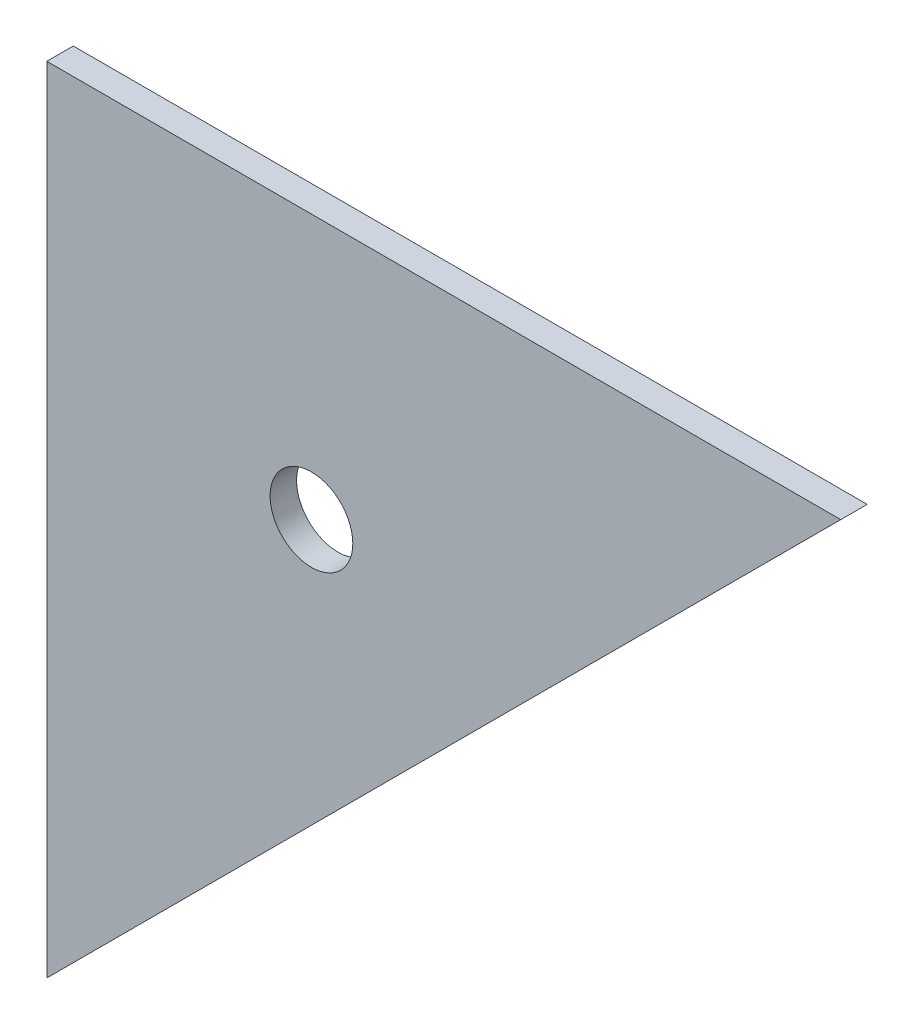
SolidWorks part; units mm, degrees
ref_plane "Front" through (0, 0, 0) normal (0, 0, 1) x (1, 0, 0)
ref_plane "Top" through (0, 0, 0) normal (0, 1, 0) x (1, 0, 0)
ref_plane "Right" through (0, 0, 0) normal (1, 0, 0) x (0, 0, -1)
sketch "Sketch1" plane through (0, 0, 0) normal (0, 0, 1) x (1, 0, 0)
  line L0 (-5.2668, 29.0495) -> (70.9332, 29.0495)
  line L1 (70.9332, 29.0495) -> (-5.2668, -47.1505)
  line L2 (-5.2668, -47.1505) -> (-5.2668, 29.0495)
extrude "Boss-Extrude1" add sketch "Sketch1" along normal blind 2.54
sketch "Sketch3" plane through (0, 0, 2.54) normal (0, 0, 1) x (1, 0, 0)
  line L0 (20.1332, 29.0495) -> (20.1332, -21.7505) construction
  line L1 (70.9332, 29.0495) -> (-5.2668, 29.0495) construction
  line L2 (-5.2668, -47.1505) -> (70.9332, 29.0495) construction
  line L3 (-5.2668, 3.6495) -> (38.3694, 3.6495) construction
  line L4 (-5.2668, 29.0495) -> (-5.2668, -47.1505) construction
  circle A0 centre (20.1332, 3.6495) radius 3.9688
  dimension "D1" = 25.4
  dimension "D2" = 25.4
extrude "Cut-Extrude3" cut sketch "Sketch3" against normal blind 101.6
